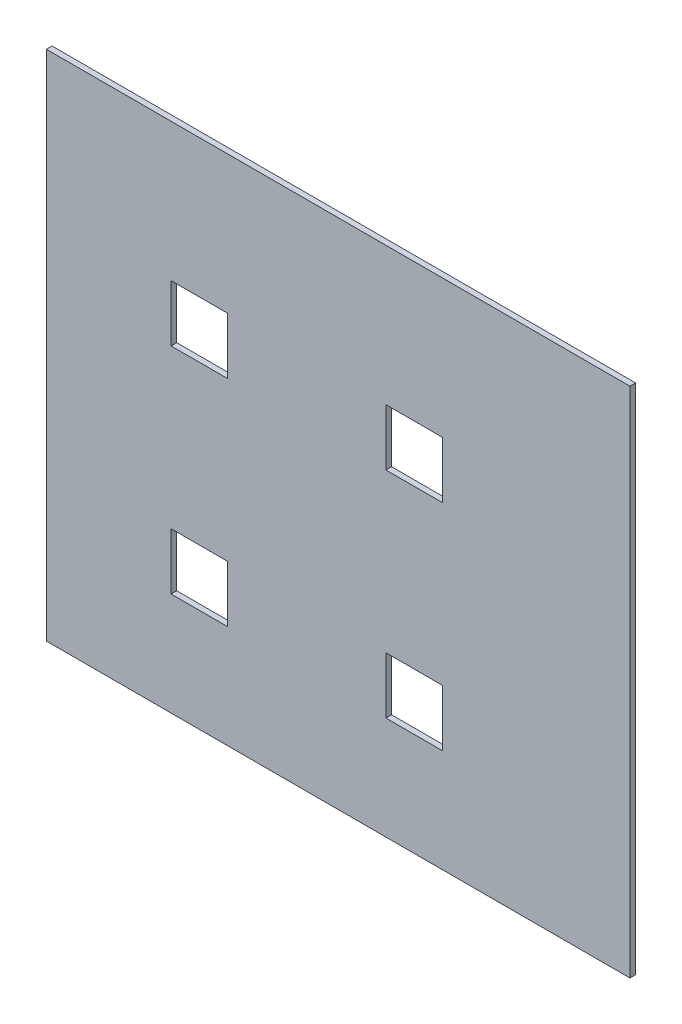
SolidWorks part; units mm, degrees
ref_plane "Plan de face" through (0, 0, 0) normal (0, 0, 1) x (1, 0, 0)
ref_plane "Plan de dessus" through (0, 0, 0) normal (0, 1, 0) x (1, 0, 0)
ref_plane "Plan de droite" through (0, 0, 0) normal (1, 0, 0) x (0, 0, -1)
sketch "Esquisse1" plane through (0, 0, 0) normal (0, 0, 1) x (1, 0, 0)
  line L1 (0, 0) -> (10, 0)
  line L2 (0, 0) -> (0, 10)
  line L3 (0, 10) -> (10, 10)
  line L4 (10, 0) -> (10, 10)
  line L5 (38, 0) -> (48, 0)
  line L6 (38, 0) -> (38, 10)
  line L7 (38, 10) -> (48, 10)
  line L8 (48, 0) -> (48, 10)
  line L9 (38, 38) -> (48, 38)
  line L10 (38, 38) -> (38, 48)
  line L11 (38, 48) -> (48, 48)
  line L12 (48, 38) -> (48, 48)
  line L13 (0, 38) -> (10, 38)
  line L14 (0, 38) -> (0, 48)
  line L15 (0, 48) -> (10, 48)
  line L16 (10, 38) -> (10, 48)
  line L17 (-22.049, 72.418) -> (81.1644, 72.418)
  line L18 (-22.049, 72.418) -> (-22.049, -18.2372)
  line L19 (-22.049, -18.2372) -> (81.1644, -18.2372)
  line L20 (81.1644, 72.418) -> (81.1644, -18.2372)
  dimension "D1" = 10
  dimension "D2" = 10
  dimension "D3" = 10
  dimension "D4" = 10
  dimension "D5" = 28
  dimension "D6" = 10
  dimension "D7" = 10
  dimension "D8" = 28
extrude "Boss.-Extru.1" add sketch "Esquisse1" along normal blind 1
